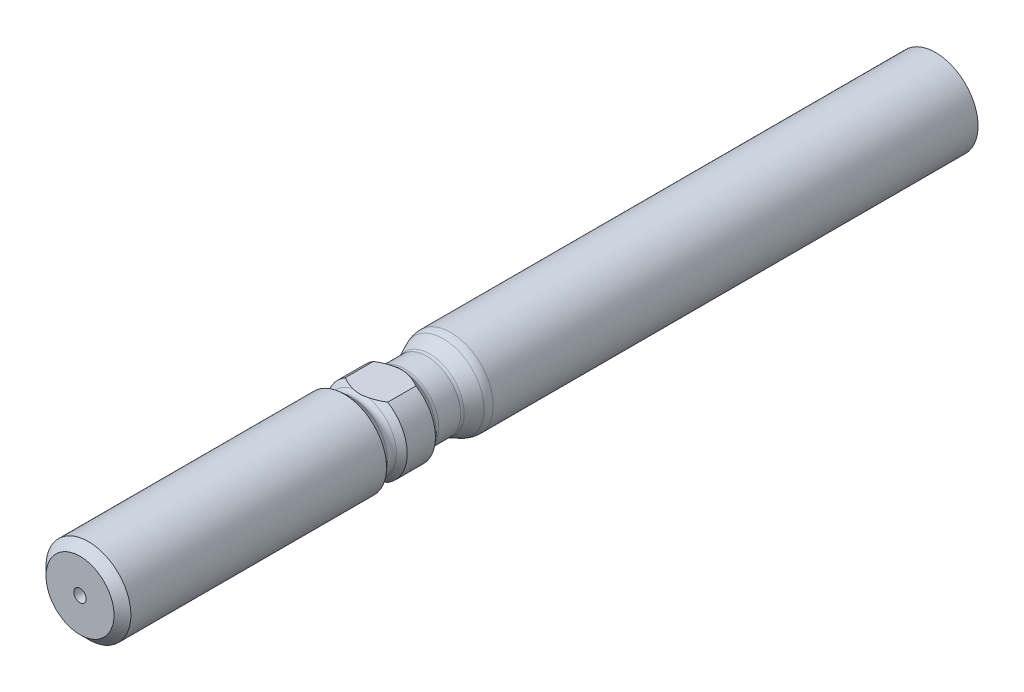
SolidWorks part; units mm, degrees
material "AISI 316 Stainless Steel Sheet (SS)"
ref_plane "Front Plane" through (0, 0, 0) normal (0, 0, 1) x (1, 0, 0)
ref_plane "Top Plane" through (0, 0, 0) normal (0, 1, 0) x (1, 0, 0)
ref_plane "Right Plane" through (0, 0, 0) normal (1, 0, 0) x (0, 0, -1)
sketch "Sketch1" plane through (0, 0, 0) normal (0, 1, 0) x (1, 0, 0)
  line L0 (0, 0) -> (0, -83.92) construction
  line L1 (0, 0) -> (4.7625, 0) construction
  line L2 (4.7625, 0) -> (4.7625, -42.325)
  line L3 (3.815, -83.92) -> (0, -83.92)
  line L5 (4.56, -52.935) -> (3.8, -52.935) construction
  line L6 (3.9952, -52.4265) -> (4.57, -51.7881)
  line L7 (3.9952, -53.4435) -> (4.7625, -54.2957)
  line L9 (4.7625, -54.2957) -> (4.7625, -82.9725)
  line L11 (4.7625, -53.6675) -> (4.7625, -54.2957) construction
  line L12 (3.815, -83.92) -> (4.7625, -82.9725)
  line L13 (4.7625, -83.92) -> (3.815, -83.92) construction
  line L14 (4.7625, -82.9725) -> (4.7625, -83.92) construction
  line L15 (4.57, -48.6181) -> (3.9876, -47.9713)
  line L16 (3.795, -47.4695) -> (3.795, -45.0095)
  line L17 (3.8653, -44.6925) -> (4.5751, -43.1702)
  line L18 (4.57, -51.7881) -> (4.57, -48.6181)
  line L19 (4.7625, -48.6358) -> (4.7625, -51.5743) construction
  line L20 (0, 0) -> (0, -83.92)
  line L21 (4.7625, 0) -> (4.7625, 12.06)
  line L22 (4.7625, 12.06) -> (0, 12.06)
  line L23 (0, 12.06) -> (0, 0)
  arc A1 (3.9952, -52.4265) -> (3.9952, -53.4435) centre (4.56, -52.935) ccw
  arc A3 (4.7625, -53.6675) -> (4.7625, -52.2025) centre (4.56, -52.935) ccw construction
  arc A4 (3.9952, -53.4435) -> (4.7625, -53.6675) centre (4.56, -52.935) ccw construction
  arc A5 (4.7625, -52.2025) -> (3.9952, -52.4265) centre (4.56, -52.935) ccw construction
  arc A6 (3.795, -45.0095) -> (3.8653, -44.6925) centre (4.545, -45.0095) cw
  arc A7 (3.9876, -47.9713) -> (3.795, -47.4695) centre (4.545, -47.4695) cw
  arc A8 (4.5751, -43.1702) -> (4.7625, -42.325) centre (2.7625, -42.325) ccw
  point P27 (3.795, -44.8432)
  dimension "D4" = 1.52
  dimension "D15" = 0.75
  dimension "D17" = 2
  dimension "D1" = 83.92
  dimension "D2" = 9.525
  dimension "D3" = 30.985
  dimension "D5" = 4.56
  dimension "D6" = 48
  dimension "D7" = 45
  dimension "D8" = 3.815
  dimension "D9" = 9.14
  dimension "D10" = 48
  dimension "D11" = 3.17
  dimension "D12" = 7.59
  dimension "D13" = 48
  dimension "D14" = 65
  dimension "D16" = 2.46
  dimension "D18" = 12.06
revolve "Revolve1" add sketch "Sketch1" angle 360 about L20
sketch "Sketch2" plane through (0, 0, 0) normal (1, 0, 0) x (0, 0, -1)
  line L0 (0, 0) -> (-83.92, 0) construction
  line L1 (-83.92, 3.815) -> (-83.92, -3.815) construction
  line L3 (-52.75, 11.9) -> (-47.75, 11.9)
  line L4 (-52.75, 11.9) -> (-52.75, 3.9)
  line L5 (-52.75, 3.9) -> (-47.75, 3.9)
  line L6 (-47.75, 11.9) -> (-47.75, 3.9)
  line L7 (-52.75, 11.9) -> (-47.75, 3.9) construction
  line L8 (-52.75, 3.9) -> (-47.75, 11.9) construction
  line L10 (-52.75, -3.9) -> (-47.75, -11.9) construction
  line L11 (-52.75, -11.9) -> (-47.75, -3.9) construction
  line L12 (-47.75, -11.9) -> (-47.75, -3.9)
  line L13 (-52.75, -3.9) -> (-47.75, -3.9)
  line L14 (-52.75, -11.9) -> (-52.75, -3.9)
  line L15 (-52.75, -11.9) -> (-47.75, -11.9)
  point P5 (-50.25, 7.9)
  point P14 (-50.25, -7.9)
  dimension "D1" = 50.25
  dimension "D2" = 8
  dimension "D3" = 5
  dimension "D4" = 3.9
extrude "Cut-Extrude3" cut sketch "Sketch2" against normal through all both and the other way through all
sketch "Sketch3" plane through (0, 0, 0) normal (1, 0, 0) x (0, 0, -1)
  line L0 (-83.92, 0) -> (-48.92, 0) construction
  line L1 (-83.92, 3.815) -> (-83.92, -3.815) construction
  dimension "D1" = 35
sketch "Sketch4" plane through (0, 0, 83.92) normal (0, 0, 1) x (1, 0, 0)
  circle A0 centre (0, 0) radius 0.7
  dimension "D1" = 1.4
extrude "Cut-Extrude4" cut sketch "Sketch4" against normal blind 10
